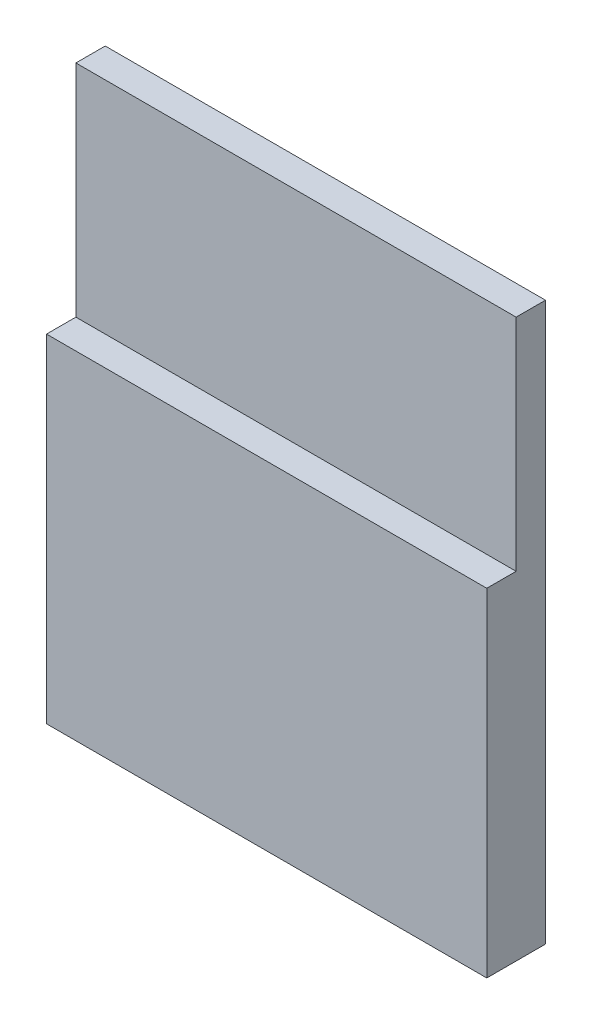
SolidWorks part; units mm, degrees
ref_plane "前视基准面" through (0, 0, 0) normal (0, 0, 1) x (1, 0, 0)
ref_plane "上视基准面" through (0, 0, 0) normal (0, 1, 0) x (1, 0, 0)
ref_plane "右视基准面" through (0, 0, 0) normal (1, 0, 0) x (0, 0, -1)
sketch "草图1" plane through (0, 0, 0) normal (0, 0, 1) x (1, 0, 0)
  line L0 (-30, 38) -> (-30, 0)
  line L1 (-30, 0) -> (0, 0)
  line L2 (0, 0) -> (0, 38)
  line L3 (0, 38) -> (-30, 38)
extrude "凸台-拉伸1" add sketch "草图1" along normal blind 2
sketch "草图2" plane through (0, 0, 2) normal (0, 0, 1) x (1, 0, 0)
  line L0 (-30, 0) -> (0, 0)
  line L1 (0, 0) -> (0, 23)
  line L2 (0, 0) -> (0, 38) construction
  line L3 (0, 23) -> (-30, 23)
  line L4 (-30, 38) -> (-30, 0) construction
  line L5 (-30, 23) -> (-30, 0)
extrude "凸台-拉伸2" add sketch "草图2" along normal blind 2
